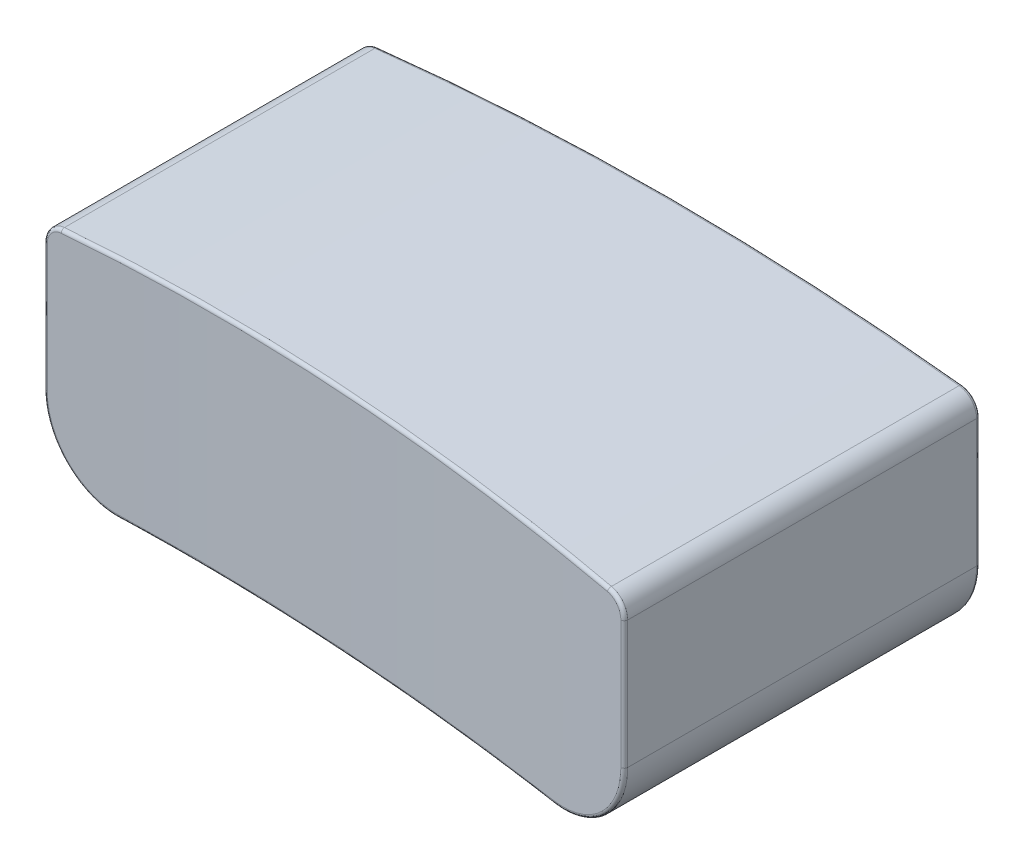
SolidWorks part; units mm, degrees
ref_plane "Front Plane" through (0, 0, 0) normal (0, 0, 1) x (1, 0, 0)
ref_plane "Top Plane" through (0, 0, 0) normal (0, 1, 0) x (1, 0, 0)
ref_plane "Right Plane" through (0, 0, 0) normal (1, 0, 0) x (0, 0, -1)
sketch "Sketch1" plane through (0, 0, 0) normal (0, 0, 1) x (1, 0, 0)
  line L0 (55, 0) -> (-55, 0) construction
  line L1 (-4.7, 1.85) -> (4.7, 1.85)
  line L2 (-4.7, 1.85) -> (-4.7, -1.85)
  line L3 (-4.7, -1.85) -> (4.7, -1.85)
  line L4 (4.7, 1.85) -> (4.7, -1.85)
  line L5 (0, -55) -> (0, 55) construction
  dimension "D1" = 9.4
  dimension "D2" = 3.7
  dimension "D3" = 1.85
  dimension "D4" = 4.7
extrude "Boss-Extrude1" add sketch "Sketch1" along normal mid plane 5.4
sketch "Sketch2" plane through (0, 0, 2.7) normal (0, 0, 1) x (1, 0, 0)
  line L0 (-4.7, 1.85) -> (-4.7, -1.85) construction
  line L1 (4.7, -1.85) -> (4.7, 1.85) construction
  line L2 (-4.7, -1.85) -> (4.7, -1.85) construction
  line L3 (4.7, 1.85) -> (-4.7, 1.85) construction
  line L4 (-4.7, 1.55) -> (-7.1207, 4.0114)
  line L5 (-7.1207, 4.0114) -> (5.5359, 3.8867)
  line L6 (5.5359, 3.8867) -> (4.7, 1.55)
  line L7 (4.7, -1.85) -> (0.3506, -3.782)
  line L8 (-4.7, -1.85) -> (0.3506, -3.782)
  arc A0 (-4.7, 1.55) -> (4.7, 1.55) centre (0, -38.1729) cw
  arc A1 (-4.7, -1.85) -> (4.7, -1.85) centre (0, -51.6286) cw
  dimension "D4" = 40
  dimension "D5" = 50
  dimension "D1" = 0
  dimension "D2" = 0.3
  dimension "D3" = 0.3
extrude "Cut-Extrude1" cut sketch "Sketch2" against normal mid plane 15.2
fillet "Fillet1" radius 1.1 2 edges at (4.7, -1.85, 0) (-4.7, -1.85, 0)
fillet "Fillet2" radius 0.3 2 edges at (4.7, 1.55, 0) (-4.7, 1.55, 0)
sketch "Sketch3" plane through (0, 0, 2.7) normal (0, 0, 1) x (1, 0, 0)
  line L0 (0, -1.9705) -> (0, 1.9705) construction
  line L1 (2.97, 0) -> (-2.97, 0) construction
  circle A0 centre (3.7, -0.6) radius 0.5
  circle A1 centre (-3.7, -0.6) radius 0.5
  dimension "D1" = 1
  dimension "D3" = 1
  dimension "D4" = 0.6
  dimension "D5" = 0.6
  dimension "D6" = 3.7
  dimension "D2" = 3.7
extrude "Cut-Extrude2" cut sketch "Sketch3" against normal blind 13 from offset 1 offset against normal yes
fillet "Fillet4" radius 0.02 2 edges at (4.2, -0.6, -2.7) (-3.2, -0.6, -2.7)
sketch "Sketch4" plane through (0, 0, 0) normal (0, 1, 0) x (1, 0, 0)
  line L0 (4.4332, 2.7) -> (-4.4332, 2.7) construction
  line L2 (0, -1.9705) -> (0, 1.9705) construction
  line L7 (-4.7, -2.1) -> (-6.6127, -3.7139)
  line L8 (-6.6127, -3.7139) -> (6.4207, -4.5741)
  line L9 (6.4207, -4.5741) -> (4.7, -2.7)
  arc A1 (4.7, -2.7) -> (-4.7, -2.1) centre (-9.5503, -152.0216) ccw
  dimension "D3" = 150
  dimension "D1" = 4.8
  dimension "D2" = 5.4
  dimension "D4" = 4.7
extrude "Cut-Extrude3" cut sketch "Sketch4" against normal mid plane 10
fillet "Fillet5" radius 0.05 17 edges at (-4.6123, 1.4945, 2.1029) (4.6236, 1.4825, -2.7) (-4.6236, 1.4825, -2.7) (4.3499, -1.4603, -2.7) (-4.3499, -1.4603, -2.7) (4.7, 0.3135, 2.7) (4.7, 0.3135, -2.7) (-4.7, 0.3135, -2.7) (0, 1.8271, -2.7) (0, -1.6286, -2.7) (4.2, -0.6, 1.7) (4.2273, -1.5592, 2.6556) (-4.4592, -1.3425, 2.108) (4.6348, 1.4693, 2.6938) (-4.7, 0.3135, 2.1)
sketch "Sketch5" plane through (0, 0, 0) normal (0, 1, 0) x (1, 0, 0)
  line L0 (3.526, 2.7) -> (-3.526, 2.7) construction
  line L1 (-4.7, -2.0516) -> (-4.7, 2.65) construction
  circle A0 centre (-0.7, 1.2) radius 0.4
  dimension "D1" = 0.8
  dimension "D3" = 4
  dimension "D2" = 1.5
extrude "Cut-Extrude4" cut sketch "Sketch5" along normal offset from surface (9.7665 mm away) 0.4 from offset 11 offset against normal yes
fillet "Fillet6" radius 0.05 1 edges at (-0.792, -1.6349, -0.8107)
